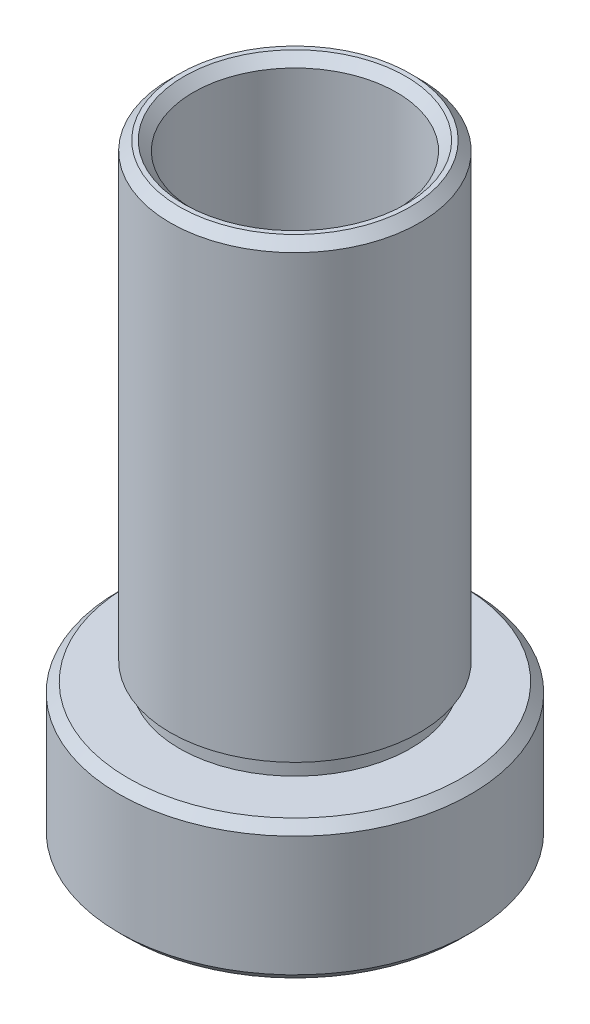
SolidWorks part; units mm, degrees
ref_plane "前视基准面" through (0, 0, 0) normal (0, 0, 1) x (1, 0, 0)
ref_plane "上视基准面" through (0, 0, 0) normal (0, 1, 0) x (1, 0, 0)
ref_plane "右视基准面" through (0, 0, 0) normal (1, 0, 0) x (0, 0, -1)
sketch "草图1" plane through (0, 0, 0) normal (0, 0, 1) x (1, 0, 0)
  line L0 (0, 44.5986) -> (0, -38.4055) construction
  line L1 (6, 27.0429) -> (6.25, 27.0429)
  line L2 (6.75, 26.5429) -> (6.75, 2.6429)
  line L3 (6.75, 2.6429) -> (6.25, 2.6429)
  line L4 (6.25, 2.6429) -> (6.25, 1.6429)
  line L5 (6.25, 1.6429) -> (9.025, 1.6429)
  line L6 (9.525, 1.1429) -> (9.525, -5.3571)
  line L7 (9.025, -5.8571) -> (8, -5.8571)
  line L8 (7.5, -5.3571) -> (7.5, -1.3571)
  line L9 (7.5, -1.3571) -> (7.6, -1.3571)
  line L10 (7.6, -1.3571) -> (7.6, -0.3571)
  line L11 (9.525, -5.3571) -> (9.025, -5.8571)
  line L12 (5.5, -0.3571) -> (5.5, 26.5429)
  line L13 (7.6, -0.3571) -> (5.5, -0.3571)
  line L14 (8, -5.8571) -> (7.5, -5.3571)
  line L15 (6.25, 27.0429) -> (6.75, 26.5429)
  line L16 (5.5, 26.5429) -> (6, 27.0429)
  line L17 (9.025, 1.6429) -> (9.525, 1.1429)
  point P3 (5.5, 27.0429)
  point P4 (6.75, 27.0429)
  point P9 (9.525, -5.8571)
  point P10 (9.525, 1.6429)
  point P11 (7.5, -5.8571)
  point P13 (6.25, 2.1429)
  point P14 (7.6, -0.8571)
  dimension "D2" = 9.525
  dimension "D3" = 7.5
  dimension "D4" = 6.75
  dimension "D5" = 5.5
  dimension "D6" = 7.5
  dimension "D7" = 5.5
  dimension "D8" = 1
  dimension "D9" = 1
  dimension "D10" = 6.25
  dimension "D11" = 7.6
revolve "旋转2" add sketch "草图1" angle 360 about L0
